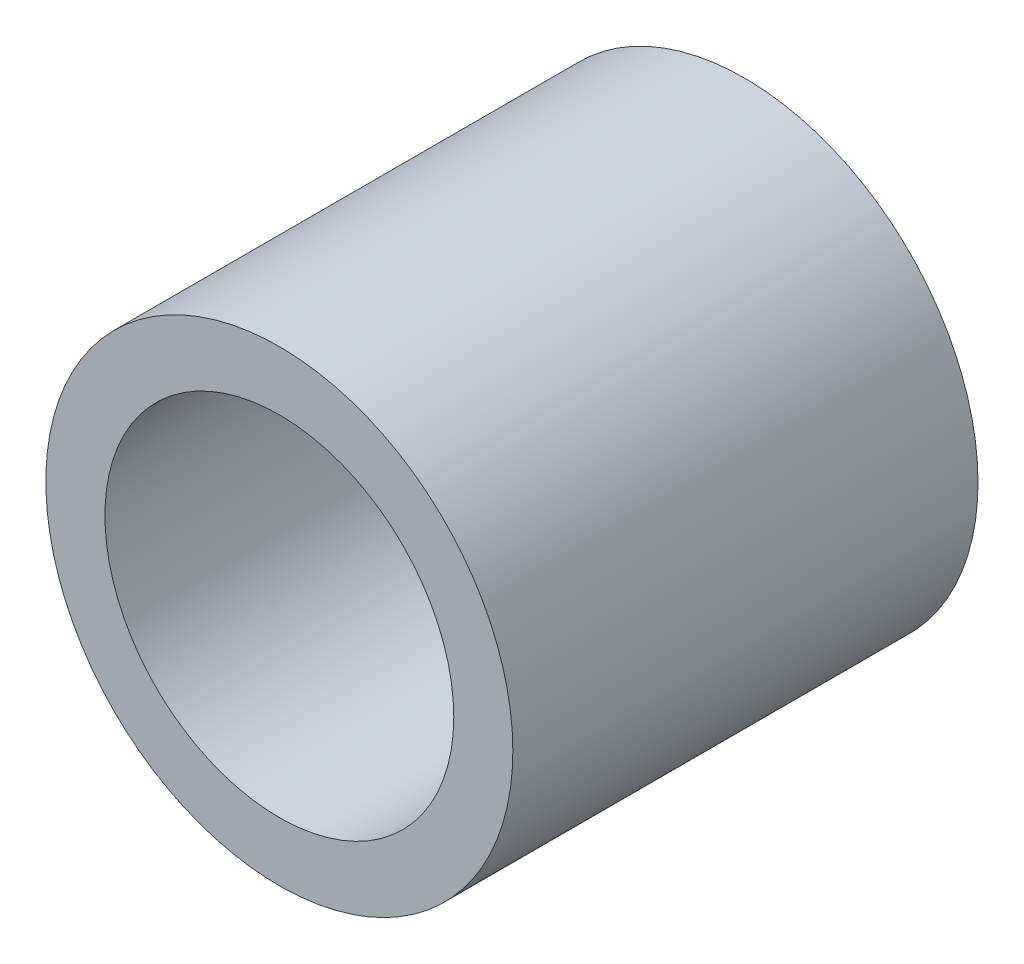
SolidWorks part; units mm, degrees
ref_plane "Front Plane" through (0, 0, 0) normal (0, 0, 1) x (1, 0, 0)
ref_plane "Top Plane" through (0, 0, 0) normal (0, 1, 0) x (1, 0, 0)
ref_plane "Right Plane" through (0, 0, 0) normal (1, 0, 0) x (0, 0, -1)
sketch "Sketch1" plane through (0, 0, 0) normal (0, 0, 1) x (1, 0, 0)
  circle A0 centre (0, 0) radius 3.1877
  circle A1 centre (0, 0) radius 2.3812
  dimension "D1" = 6.3754
  dimension "ID" = 4.7625
extrude "Extrude1" add sketch "Sketch1" along normal mid plane 6.35
sketch "Sketch2" plane through (0, 0, 0) normal (1, 0, 0) x (0, 0, -1)
  line L0 (-3.175, -2.3812) -> (3.175, -2.3812) construction
  line L3 (3.175, 2.3812) -> (-3.175, 2.3812) construction
  line L5 (-3.175, -2.3812) -> (3.175, -2.3812)
  line L6 (3.175, 2.3812) -> (-3.175, 2.3812)
sketch "Sketch4" plane through (0, 0, 3.175) normal (0, 0, 1) x (1, 0, 0)
  line L0 (0, 0) -> (-1.6838, 1.6838)
  line L1 (0, -8.7312) -> (0, 8.7312) construction
  circle A0 centre (0, 0) radius 2.3812 construction
  dimension "D1" = 45
